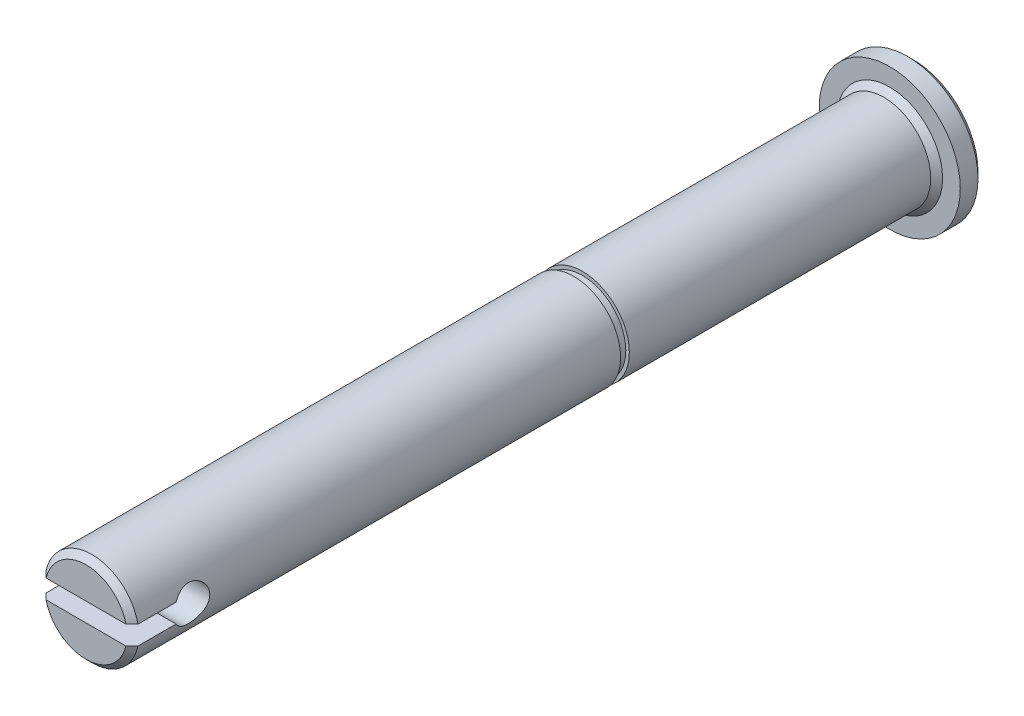
SolidWorks part; units mm, degrees
material "AISI 4340 Steel, normalized"
ref_plane "Front Plane" through (0, 0, 0) normal (0, 0, 1) x (1, 0, 0)
ref_plane "Top Plane" through (0, 0, 0) normal (0, 1, 0) x (1, 0, 0)
ref_plane "Right Plane" through (0, 0, 0) normal (1, 0, 0) x (0, 0, -1)
sketch "Sketch1" plane through (0, 0, 0) normal (1, 0, 0) x (0, 0, -1)
  line L0 (0, 3.9688) -> (-26, 3.9687)
  line L1 (-26, 3.9687) -> (-26, 3.9375)
  line L2 (-26, 3.668) -> (-26, 3.9375)
  line L3 (-68, 3.9687) -> (-68, 0)
  line L4 (-68, 0) -> (2, 0)
  line L5 (2, 0) -> (2, 5.9688)
  line L6 (2, 5.9688) -> (0, 5.9688)
  line L7 (0, 5.9688) -> (0, 3.9688)
  line L8 (-100.1071, 0) -> (6.2625, 0) construction
  line L9 (-26, 3.668) -> (-26.7366, 3.668)
  line L10 (-26.7366, 3.668) -> (-26.7366, 3.9687)
  line L11 (-26.7366, 3.9687) -> (-68, 3.9687)
  dimension "D1" = 26
  dimension "D2" = 2
  dimension "D3" = 70
  dimension "D4" = 2
  dimension "D5" = 7.9375
  dimension "D6" = 7.336
  dimension "D7" = 0.7366
revolve "Revolve1" add sketch "Sketch1"
sketch "Sketch2" plane through (0, 0, 0) normal (1, 0, 0) x (0, 0, -1)
  line L0 (11.707, 0) -> (-101.6807, 0) construction
  line L2 (-69.5615, 0.8) -> (-64.2689, 0.8)
  line L3 (-69.5615, -0.8) -> (-64.2689, -0.8)
  line L4 (-69.5615, -0.8) -> (-69.5615, 0.8)
  line L5 (-68, 3.9687) -> (-68, -3.9687) construction
  arc A0 (-64.2689, -0.8) -> (-64.2689, 0.8) centre (-63, 0) ccw
  dimension "D1" = 3
  dimension "D2" = 5
  dimension "D3" = 0.8
  dimension "D4" = 1.6
extrude "Extrude1" cut sketch "Sketch2" against normal through all and the other way through all
chamfer "Chamfer1" distance 0.5 angle 45 4 edges at (5.9688, 0, -2) (3.9688, 0, 0) (0, -3.9687, 68) (0, 3.9687, 68)
